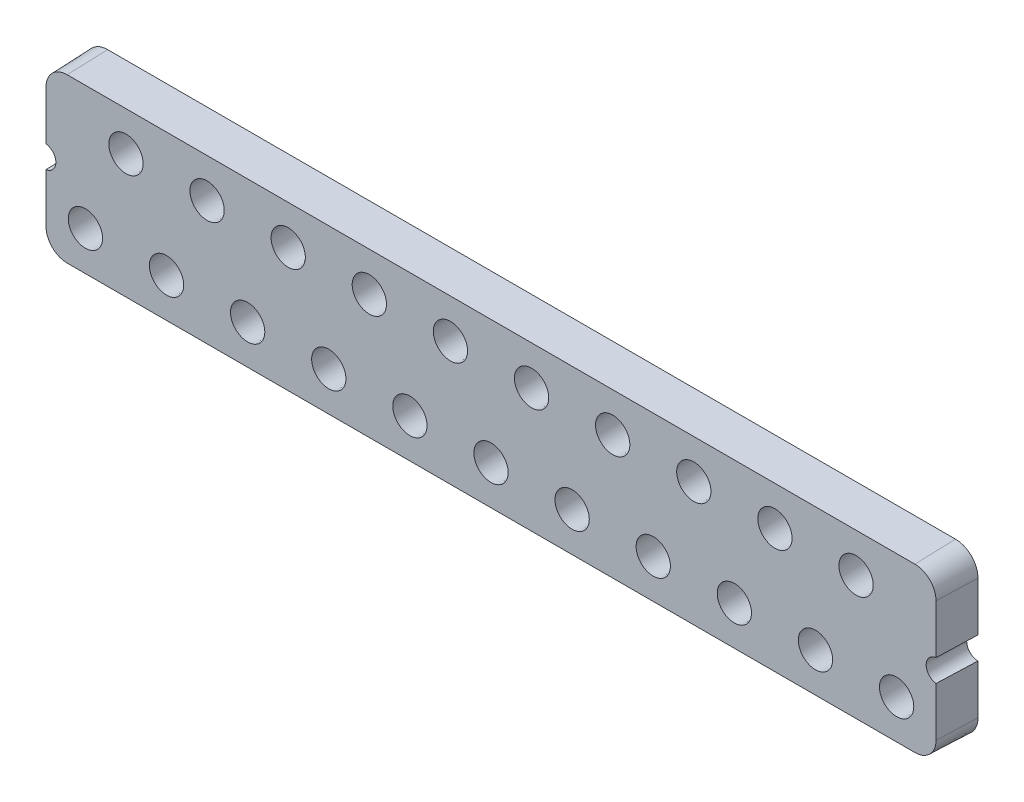
SolidWorks part; units mm, degrees
ref_plane "Front" through (0, 0, 0) normal (0, 0, 1) x (1, 0, 0)
ref_plane "Top" through (0, 0, 0) normal (0, 1, 0) x (1, 0, 0)
ref_plane "Right" through (0, 0, 0) normal (1, 0, 0) x (0, 0, -1)
sketch "Sketch11" plane through (0, 0, 0) normal (0, 0, 1) x (1, 0, 0)
  line L0 (19.812, 0.5) -> (19.812, -0.5)
  line L1 (18.812, 3.683) -> (-18.812, 3.683)
  line L2 (-19.812, 2.683) -> (-19.812, 0.5)
  line L3 (-19.812, -0.5) -> (-19.812, -2.683)
  line L4 (-18.812, -3.683) -> (18.812, -3.683)
  line L5 (19.812, -2.683) -> (19.812, -0.5)
  line L6 (19.812, 0.5) -> (19.812, 2.683)
  line L7 (-19.812, 0.5) -> (-19.812, -0.5)
  circle A0 centre (16.2, 1.885) radius 0.8 construction
  circle A1 centre (12.6, 1.885) radius 0.8 construction
  circle A2 centre (9, 1.885) radius 0.8 construction
  circle A3 centre (5.4, 1.885) radius 0.8 construction
  circle A4 centre (1.8, 1.885) radius 0.8 construction
  circle A5 centre (-1.8, 1.885) radius 0.8 construction
  circle A6 centre (-5.4, 1.885) radius 0.8 construction
  circle A7 centre (-9, 1.885) radius 0.8 construction
  circle A8 centre (-12.6, 1.885) radius 0.8 construction
  circle A9 centre (-16.2, 1.885) radius 0.8 construction
  circle A10 centre (-18, -1.885) radius 0.8 construction
  circle A11 centre (-14.4, -1.885) radius 0.8 construction
  circle A12 centre (-10.8, -1.885) radius 0.8 construction
  circle A13 centre (-7.2, -1.885) radius 0.8 construction
  circle A14 centre (-3.6, -1.885) radius 0.8 construction
  circle A15 centre (0, -1.885) radius 0.8 construction
  circle A16 centre (3.6, -1.885) radius 0.8 construction
  circle A17 centre (7.2, -1.885) radius 0.8 construction
  circle A18 centre (10.8, -1.885) radius 0.8 construction
  circle A19 centre (14.4, -1.885) radius 0.8 construction
  circle A20 centre (18, -1.885) radius 0.8 construction
  arc A21 (-19.812, 0.5) -> (-19.812, -0.5) centre (-19.812, 0) cw construction
  arc A22 (-18.812, 3.683) -> (-19.812, 2.683) centre (-18.812, 2.683) ccw
  arc A23 (-19.812, -2.683) -> (-18.812, -3.683) centre (-18.812, -2.683) ccw
  arc A24 (18.812, -3.683) -> (19.812, -2.683) centre (18.812, -2.683) ccw
  arc A25 (19.812, -0.5) -> (19.812, 0.5) centre (19.812, 0) cw construction
  arc A26 (19.812, 2.683) -> (18.812, 3.683) centre (18.812, 2.683) ccw
  circle A27 centre (16.2, 1.885) radius 1.205 construction
  circle A28 centre (12.6, 1.885) radius 1.205 construction
  circle A29 centre (9, 1.885) radius 1.205 construction
  circle A30 centre (5.4, 1.885) radius 1.205 construction
  circle A31 centre (1.8, 1.885) radius 1.205 construction
  circle A32 centre (-1.8, 1.885) radius 1.205 construction
  circle A33 centre (-5.4, 1.885) radius 1.205 construction
  circle A34 centre (-9, 1.885) radius 1.205 construction
  circle A35 centre (-12.6, 1.885) radius 1.205 construction
  circle A36 centre (-16.2, 1.885) radius 1.205 construction
  circle A37 centre (-18, -1.885) radius 1.205 construction
  circle A38 centre (-14.4, -1.885) radius 1.205 construction
  circle A39 centre (-10.8, -1.885) radius 1.205 construction
  circle A40 centre (-7.2, -1.885) radius 1.205 construction
  circle A41 centre (-3.6, -1.885) radius 1.205 construction
  circle A42 centre (0, -1.885) radius 1.205 construction
  circle A43 centre (3.6, -1.885) radius 1.205 construction
  circle A44 centre (7.2, -1.885) radius 1.205 construction
  circle A45 centre (10.8, -1.885) radius 1.205 construction
  circle A46 centre (14.4, -1.885) radius 1.205 construction
  circle A47 centre (18, -1.885) radius 1.205 construction
extrude "Boss-Extrude1" add sketch "Sketch11" along normal blind 1.8 draft 2
sketch "Sketch10" plane through (0, 0, 0) normal (0, 0, 1) x (1, 0, 0)
  line L1 (18.812, 3.683) -> (-18.812, 3.683) construction
  line L2 (-19.812, 2.683) -> (-19.812, 0.5) construction
  line L3 (-19.812, -0.5) -> (-19.812, -2.683) construction
  line L4 (-18.812, -3.683) -> (18.812, -3.683) construction
  line L5 (19.812, -2.683) -> (19.812, -0.5) construction
  line L6 (19.812, 0.5) -> (19.812, 2.683) construction
  circle A0 centre (16.2, 1.885) radius 0.805 construction
  circle A1 centre (12.6, 1.885) radius 0.805 construction
  circle A2 centre (9, 1.885) radius 0.805 construction
  circle A3 centre (5.4, 1.885) radius 0.805 construction
  circle A4 centre (1.8, 1.885) radius 0.805 construction
  circle A5 centre (-1.8, 1.885) radius 0.805 construction
  circle A6 centre (-5.4, 1.885) radius 0.805 construction
  circle A7 centre (-9, 1.885) radius 0.805 construction
  circle A8 centre (-12.6, 1.885) radius 0.805 construction
  circle A9 centre (-16.2, 1.885) radius 0.805 construction
  circle A10 centre (-18, -1.885) radius 0.805 construction
  circle A11 centre (-14.4, -1.885) radius 0.805 construction
  circle A12 centre (-10.8, -1.885) radius 0.805 construction
  circle A13 centre (-7.2, -1.885) radius 0.805 construction
  circle A14 centre (-3.6, -1.885) radius 0.805 construction
  circle A15 centre (0, -1.885) radius 0.805 construction
  circle A16 centre (3.6, -1.885) radius 0.805 construction
  circle A17 centre (7.2, -1.885) radius 0.805 construction
  circle A18 centre (10.8, -1.885) radius 0.805 construction
  circle A19 centre (14.4, -1.885) radius 0.805 construction
  circle A20 centre (18, -1.885) radius 0.805 construction
  arc A21 (-19.812, 0.5) -> (-19.812, -0.5) centre (-19.812, 0) cw construction
  arc A22 (-18.812, 3.683) -> (-19.812, 2.683) centre (-18.812, 2.683) ccw construction
  arc A23 (-19.812, -2.683) -> (-18.812, -3.683) centre (-18.812, -2.683) ccw construction
  arc A24 (18.812, -3.683) -> (19.812, -2.683) centre (18.812, -2.683) ccw construction
  arc A25 (19.812, -0.5) -> (19.812, 0.5) centre (19.812, 0) cw construction
  arc A26 (19.812, 2.683) -> (18.812, 3.683) centre (18.812, 2.683) ccw construction
  circle A27 centre (16.2, 1.885) radius 1.223
  circle A28 centre (12.6, 1.885) radius 1.223
  circle A29 centre (9, 1.885) radius 1.223
  circle A30 centre (5.4, 1.885) radius 1.223
  circle A31 centre (1.8, 1.885) radius 1.223
  circle A32 centre (-1.8, 1.885) radius 1.223
  circle A33 centre (-5.4, 1.885) radius 1.223
  circle A34 centre (-9, 1.885) radius 1.223
  circle A35 centre (-12.6, 1.885) radius 1.223
  circle A36 centre (-16.2, 1.885) radius 1.223
  circle A37 centre (-18, -1.885) radius 1.223
  circle A38 centre (-14.4, -1.885) radius 1.223
  circle A39 centre (-10.8, -1.885) radius 1.223
  circle A40 centre (-7.2, -1.885) radius 1.223
  circle A41 centre (-3.6, -1.885) radius 1.223
  circle A42 centre (0, -1.885) radius 1.223
  circle A43 centre (3.6, -1.885) radius 1.223
  circle A44 centre (7.2, -1.885) radius 1.223
  circle A45 centre (10.8, -1.885) radius 1.223
  circle A46 centre (14.4, -1.885) radius 1.223
  circle A47 centre (18, -1.885) radius 1.223
extrude "Cut-Extrude2" cut sketch "Sketch10" along normal blind 0.25 draft 2
sketch "Sketch9" plane through (0, 0, 0.25) normal (0, 0, 1) x (1, 0, 0)
  line L1 (18.812, 3.683) -> (-18.812, 3.683) construction
  line L2 (-19.812, 2.683) -> (-19.812, 0.5) construction
  line L3 (-19.812, -0.5) -> (-19.812, -2.683) construction
  line L4 (-18.812, -3.683) -> (18.812, -3.683) construction
  line L5 (19.812, -2.683) -> (19.812, -0.5) construction
  line L6 (19.812, 0.5) -> (19.812, 2.683) construction
  circle A0 centre (16.2, 1.885) radius 0.815
  circle A1 centre (12.6, 1.885) radius 0.815
  circle A2 centre (9, 1.885) radius 0.815
  circle A3 centre (5.4, 1.885) radius 0.815
  circle A4 centre (1.8, 1.885) radius 0.815
  circle A5 centre (-1.8, 1.885) radius 0.815
  circle A6 centre (-5.4, 1.885) radius 0.815
  circle A7 centre (-9, 1.885) radius 0.815
  circle A8 centre (-12.6, 1.885) radius 0.815
  circle A9 centre (-16.2, 1.885) radius 0.815
  circle A10 centre (-18, -1.885) radius 0.815
  circle A11 centre (-14.4, -1.885) radius 0.815
  circle A12 centre (-10.8, -1.885) radius 0.815
  circle A13 centre (-7.2, -1.885) radius 0.815
  circle A14 centre (-3.6, -1.885) radius 0.815
  circle A15 centre (0, -1.885) radius 0.815
  circle A16 centre (3.6, -1.885) radius 0.815
  circle A17 centre (7.2, -1.885) radius 0.815
  circle A18 centre (10.8, -1.885) radius 0.815
  circle A19 centre (14.4, -1.885) radius 0.815
  circle A20 centre (18, -1.885) radius 0.815
  arc A21 (-19.812, 0.5) -> (-19.812, -0.5) centre (-19.812, 0) cw construction
  arc A22 (-18.812, 3.683) -> (-19.812, 2.683) centre (-18.812, 2.683) ccw construction
  arc A23 (-19.812, -2.683) -> (-18.812, -3.683) centre (-18.812, -2.683) ccw construction
  arc A24 (18.812, -3.683) -> (19.812, -2.683) centre (18.812, -2.683) ccw construction
  arc A25 (19.812, -0.5) -> (19.812, 0.5) centre (19.812, 0) cw construction
  arc A26 (19.812, 2.683) -> (18.812, 3.683) centre (18.812, 2.683) ccw construction
  circle A27 centre (16.2, 1.885) radius 1.205 construction
  circle A28 centre (12.6, 1.885) radius 1.205 construction
  circle A29 centre (9, 1.885) radius 1.205 construction
  circle A30 centre (5.4, 1.885) radius 1.205 construction
  circle A31 centre (1.8, 1.885) radius 1.205 construction
  circle A32 centre (-1.8, 1.885) radius 1.205 construction
  circle A33 centre (-5.4, 1.885) radius 1.205 construction
  circle A34 centre (-9, 1.885) radius 1.205 construction
  circle A35 centre (-12.6, 1.885) radius 1.205 construction
  circle A36 centre (-16.2, 1.885) radius 1.205 construction
  circle A37 centre (-18, -1.885) radius 1.205 construction
  circle A38 centre (-14.4, -1.885) radius 1.205 construction
  circle A39 centre (-10.8, -1.885) radius 1.205 construction
  circle A40 centre (-7.2, -1.885) radius 1.205 construction
  circle A41 centre (-3.6, -1.885) radius 1.205 construction
  circle A42 centre (0, -1.885) radius 1.205 construction
  circle A43 centre (3.6, -1.885) radius 1.205 construction
  circle A44 centre (7.2, -1.885) radius 1.205 construction
  circle A45 centre (10.8, -1.885) radius 1.205 construction
  circle A46 centre (14.4, -1.885) radius 1.205 construction
  circle A47 centre (18, -1.885) radius 1.205 construction
extrude "Cut-Extrude3" cut sketch "Sketch9" along normal through all draft 2
sketch "Sketch12" plane through (0, 0, 0) normal (0, 0, 1) x (1, 0, 0)
  line L1 (19.812, -2.683) -> (19.812, 2.683) construction
  line L2 (-19.812, 2.683) -> (-19.812, -2.683) construction
  circle A0 centre (19.812, 0) radius 0.5
  circle A1 centre (-19.812, 0) radius 0.5
extrude "Cut-Extrude4" cut sketch "Sketch12" along normal through all
